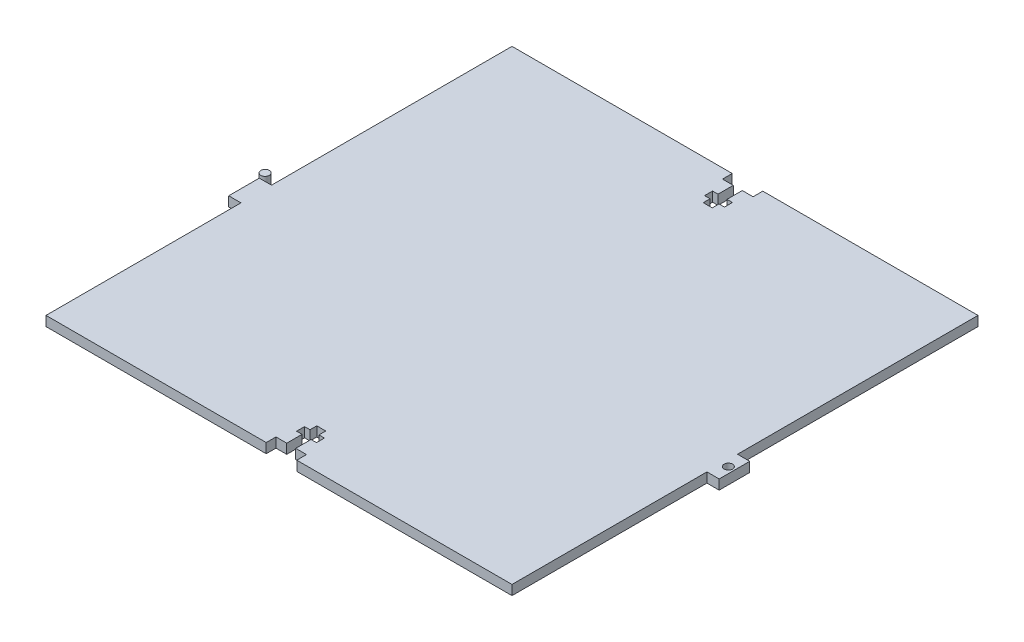
SolidWorks part; units mm, degrees
ref_plane "Front Plane" through (0, 0, 0) normal (0, 0, 1) x (1, 0, 0)
ref_plane "Top Plane" through (0, 0, 0) normal (0, 1, 0) x (1, 0, 0)
ref_plane "Right Plane" through (0, 0, 0) normal (1, 0, 0) x (0, 0, -1)
sketch "Sketch1" plane through (0, 0, 0) normal (0, 1, 0) x (1, 0, 0)
  line L1 (-77.02, 76.2) -> (-5.2921, 76.2)
  line L2 (-77.02, 76.2) -> (-77.02, -2.4489)
  line L3 (-77.02, -76.2) -> (-5.2921, -76.2)
  line L4 (75.38, 76.2) -> (75.38, -2.4489)
  line L5 (3.6521, -76.2) -> (-5.2921, -76.2)
  line L6 (-5.2921, 76.2) -> (3.6521, 76.2)
  line L16 (-81.02, -7.4489) -> (79.38, -7.4489) construction
  line L17 (-81.5456, 1.4) -> (-81.5456, -1.4) construction
  line L18 (-81.02, -2.4489) -> (-77.02, -2.4489)
  line L19 (77.38, -2.4489) -> (77.38, -12.4489) construction
  line L21 (-81.02, -2.4489) -> (-81.02, -12.4489)
  line L24 (-81.02, -12.4489) -> (-77.02, -12.4489)
  line L26 (-82.9456, 0) -> (-80.1456, 0) construction
  line L28 (75.38, -2.4489) -> (79.38, -2.4489)
  line L30 (75.38, -12.4489) -> (79.38, -12.4489)
  line L31 (79.38, -2.4489) -> (79.38, -12.4489)
  line L42 (3.6521, 76.2) -> (75.38, 76.2)
  line L43 (3.6521, -76.2) -> (75.38, -76.2)
  line L45 (75.38, -12.4489) -> (75.38, -76.2)
  line L47 (-77.02, -12.4489) -> (-77.02, -76.2)
  circle A0 centre (-81.5456, 0) radius 1.4
  circle A3 centre (77.38, -7.4489) radius 1.4
  point P0 (0, 0)
  point P9 (0, 63.7717)
  point P43 (0, -67.5894)
  dimension "D4" = 2.8
  dimension "D5" = 2.8
  dimension "D7" = 4
  dimension "D1" = 152.4
  dimension "D2" = 152.4
  dimension "D3" = 10
  dimension "D6" = 4
  dimension "D8" = 10
extrude "Boss-Extrude1" add sketch "Sketch1" along normal blind 3.18
sketch "Sketch2" plane through (0, 3.18, 0) normal (0, 1, 0) x (1, 0, 0)
  line L0 (75.38, 76.2) -> (-77.02, 76.2) construction
  line L1 (5, 76.2) -> (-5, 76.2)
  line L2 (5, 76.2) -> (5, 73.02)
  line L3 (5, 73.02) -> (1.47, 73.02)
  line L4 (-5, 76.2) -> (-5, 73.02)
  line L5 (0, 0) -> (0, 76.2) construction
  line L7 (1.47, 73.02) -> (1.47, 68.02)
  line L8 (1.47, 63.2) -> (-1.47, 63.2)
  line L9 (-1.47, 73.02) -> (-1.47, 68.02)
  line L10 (3.25, 68.02) -> (1.47, 68.02)
  line L11 (3.25, 68.02) -> (3.25, 65.42)
  line L12 (3.25, 65.42) -> (1.47, 65.42)
  line L13 (-3.25, 68.02) -> (-3.25, 65.42)
  line L14 (-1.47, 73.02) -> (-5, 73.02)
  line L15 (-1.47, 68.02) -> (-3.25, 68.02)
  line L16 (-1.47, 65.42) -> (-3.25, 65.42)
  line L17 (-1.47, 65.42) -> (-1.47, 63.2)
  line L18 (1.47, 65.42) -> (1.47, 63.2)
  dimension "D1" = 2.94
  dimension "D2" = 6.5
  dimension "D3" = 2.6
  dimension "D4" = 13
  dimension "D5" = 3.18
  dimension "D6" = 10
  dimension "D7" = 5
extrude "Cut-Extrude1" cut sketch "Sketch2" against normal blind 3.18
mirror "Mirror4" about plane through (0, 0, 0) normal (0, 0, 1) of "Cut-Extrude1"
